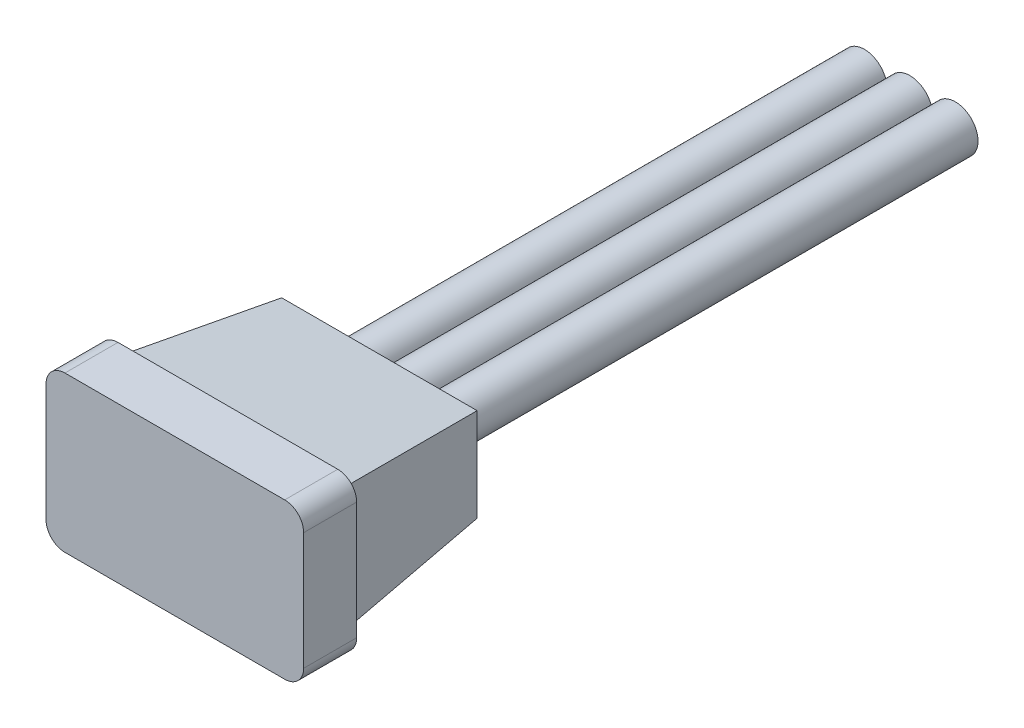
SolidWorks part; units mm, degrees
ref_plane "Front Plane" through (0, 0, 0) normal (0, 0, 1) x (1, 0, 0)
ref_plane "Top Plane" through (0, 0, 0) normal (0, 1, 0) x (1, 0, 0)
ref_plane "Right Plane" through (0, 0, 0) normal (1, 0, 0) x (0, 0, -1)
sketch "BaseS" plane through (0, 0, 0) normal (0, 0, 1) x (1, 0, 0)
  line L0 (-3.4, 2.05) -> (3.4, 2.05)
  line L1 (-3.4, 2.05) -> (-3.4, -2.05)
  line L2 (-3.4, -2.05) -> (3.4, -2.05)
  line L3 (3.4, 2.05) -> (3.4, -2.05)
  line L4 (-3.4, 2.05) -> (3.4, -2.05) construction
  line L5 (-3.4, -2.05) -> (3.4, 2.05) construction
  point P0 (0, 0)
  dimension "Width" = 6.8
  dimension "Height" = 4.1
extrude "BASE" add sketch "BaseS" against normal blind 1.4
sketch "ExtendedBodyS" plane through (0, 0, -1.4) normal (0, 0, -1) x (-1, 0, 0)
  line L0 (-3, 1.65) -> (-3, -1.65)
  line L1 (-3, -1.65) -> (3, -1.65)
  line L2 (3, -1.65) -> (3, 1.65)
  line L3 (3, 1.65) -> (-3, 1.65)
  line L4 (-3.4, 2.05) -> (-3.4, -2.05)
  line L5 (-3.4, -2.05) -> (3.4, -2.05)
  line L6 (3.4, -2.05) -> (3.4, 2.05)
  line L7 (3.4, 2.05) -> (-3.4, 2.05)
  line L8 (-3.4, 2.05) -> (-3.4, -2.05) construction
  line L9 (-3.4, -2.05) -> (3.4, -2.05) construction
  line L10 (3.4, -2.05) -> (3.4, 2.05) construction
  line L11 (3.4, 2.05) -> (-3.4, 2.05) construction
  dimension "D1" = 0
  dimension "WidthControl" = 0.4
extrude "EXTENDED BODY" add sketch "ExtendedBodyS" along normal blind 4 draft 6
sketch "PositiveS" plane through (0, 0, -5.4) normal (0, 0, -1) x (-1, 0, 0)
  circle A0 centre (0, 0) radius 0.6
  dimension "Dia" = 1.2
extrude "POSITIVE" add sketch "PositiveS" along normal blind 14
sketch "SignalS" plane through (0, 0, -5.4) normal (0, 0, -1) x (-1, 0, 0)
  line L0 (0, 0) -> (1.2, 0) construction
  circle A0 centre (1.2, 0) radius 0.6
  circle A1 centre (0, 0) radius 0.6 construction
extrude "SIGNAL" add sketch "SignalS" along normal up to surface (14 mm away) separate body up to face at (-0.6, 0, -19.4)
sketch "NegativeS" plane through (0, 0, -5.4) normal (0, 0, -1) x (-1, 0, 0)
  line L0 (0, 0) -> (-1.2, 0) construction
  circle A0 centre (-1.2, 0) radius 0.6
  circle A1 centre (0, 0) radius 0.6 construction
extrude "NEGATIVE" add sketch "NegativeS" along normal up to surface (14 mm away) separate body up to face at (-0.6, 0, -19.4)
fillet "BASE F" radius 0.5 4 edges at (-3.4, -2.05, -0.7) (-3.4, 2.05, -0.7) (3.4, -2.05, -0.7) (3.4, 2.05, -0.7)
